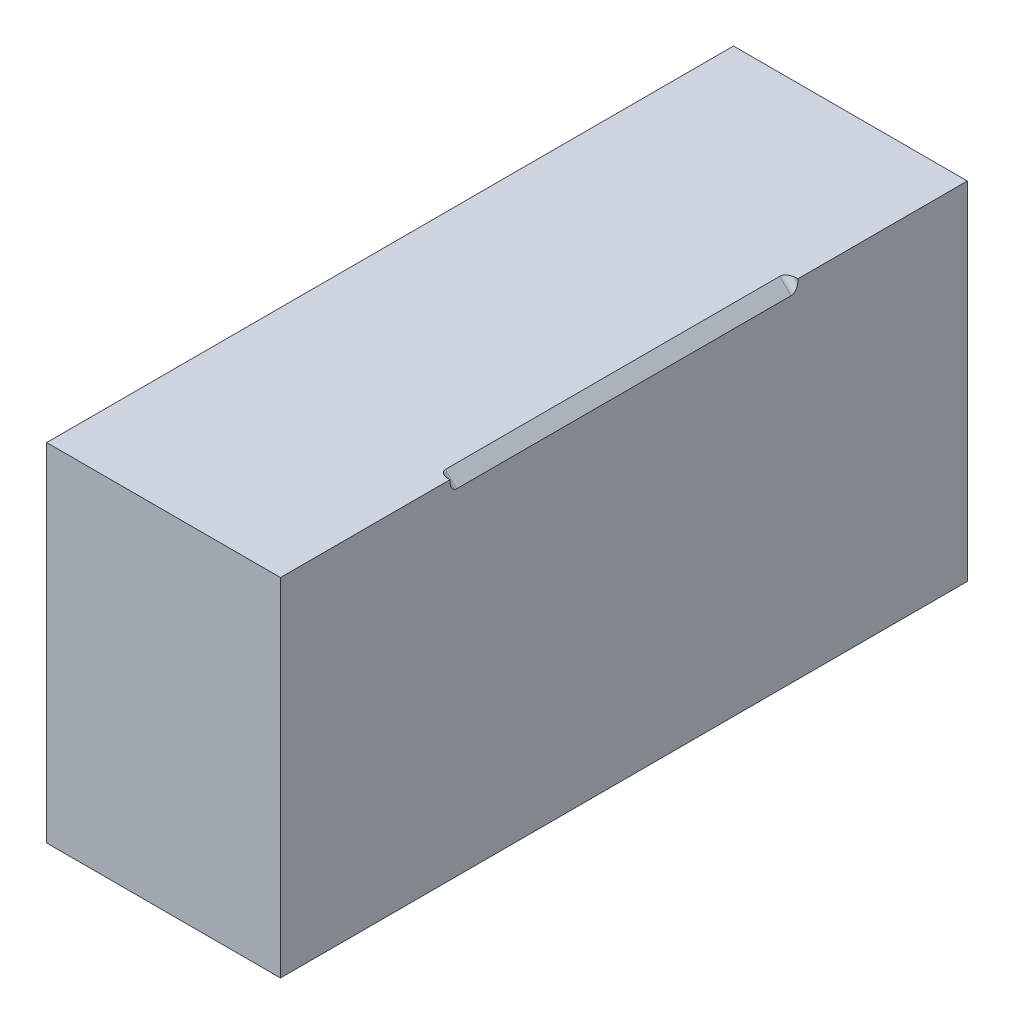
SolidWorks part; units mm, degrees
ref_plane "Ebene vorne" through (0, 0, 0) normal (0, 0, 1) x (1, 0, 0)
ref_plane "Ebene oben" through (0, 0, 0) normal (0, 1, 0) x (1, 0, 0)
ref_plane "Ebene rechts" through (0, 0, 0) normal (1, 0, 0) x (0, 0, -1)
sketch "Skizze1" plane through (0, 0, 0) normal (0, 0, 1) x (1, 0, 0)
  line L1 (52.0808, -77.2533) -> (-52.0808, -77.2533)
  line L2 (52.0808, -77.2533) -> (52.0808, 77.2533)
  line L3 (52.0808, 77.2533) -> (-52.0808, 77.2533)
  line L4 (-52.0808, -77.2533) -> (-52.0808, 77.2533)
  line L5 (52.0808, -77.2533) -> (-52.0808, 77.2533) construction
  line L6 (52.0808, 77.2533) -> (-52.0808, -77.2533) construction
  point P0 (0, 0)
  dimension "D1" = 104.1615
  dimension "D2" = 154.5066
extrude "Aufsatz-Linear austragen1" add sketch "Skizze1" along normal mid plane 306
sketch "Skizze2" plane through (0, 0, 0) normal (0, 0, 1) x (1, 0, 0)
  line L0 (47.0808, 77.2533) -> (52.0808, 77.2533)
  line L1 (52.0808, 77.2533) -> (52.0808, 72.2533)
  line L2 (52.0808, 72.2533) -> (47.0808, 77.2533)
  dimension "D1" = 5
extrude "Schnitt-Linear austragen1" cut sketch "Skizze2" against normal mid plane 155
fillet "Verrundung3" radius 3 2 edges at (49.5808, 74.7533, 77.5) (49.5808, 74.7533, -77.5)
other "Fläche löschen1" [suppressed]
